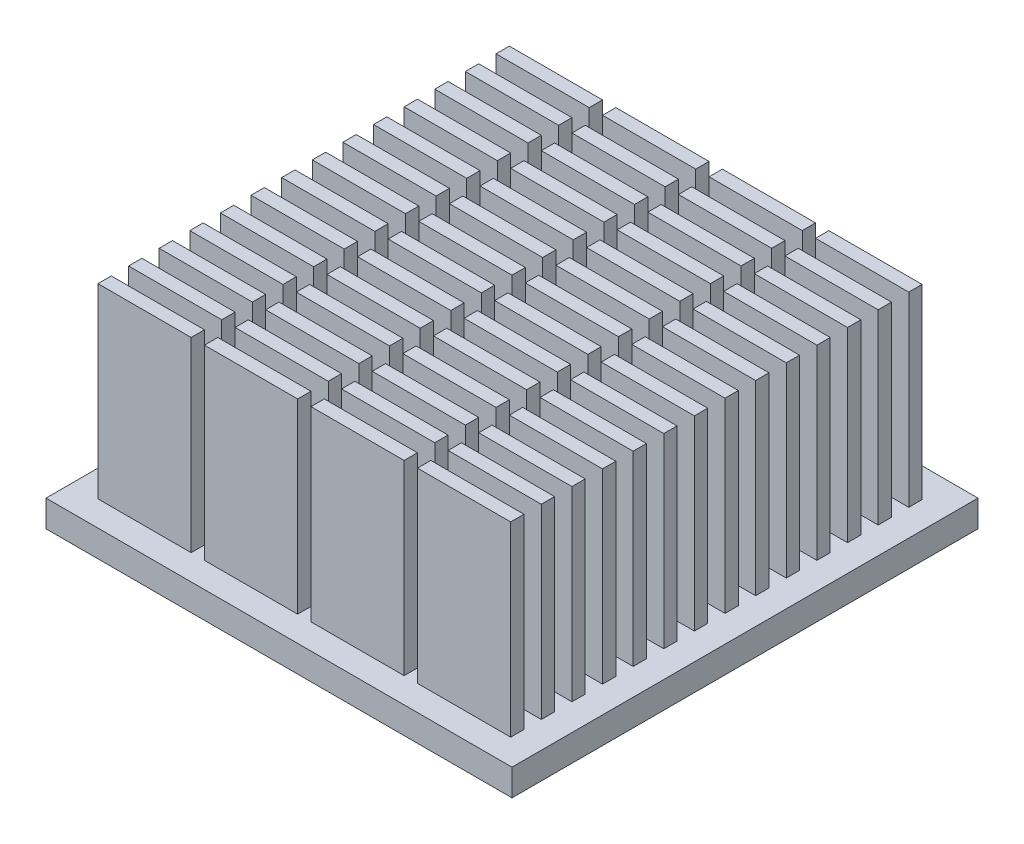
SolidWorks part; units mm, degrees
ref_plane "Front Plane" through (0, 0, 0) normal (0, 0, 1) x (1, 0, 0)
ref_plane "Top Plane" through (0, 0, 0) normal (0, 1, 0) x (1, 0, 0)
ref_plane "Right Plane" through (0, 0, 0) normal (1, 0, 0) x (0, 0, -1)
sketch "Sketch1" plane through (0, 0, 0) normal (0, 1, 0) x (1, 0, 0)
  line L1 (-17.5, -17.5) -> (17.5, -17.5)
  line L2 (-17.5, -17.5) -> (-17.5, 17.5)
  line L3 (-17.5, 17.5) -> (17.5, 17.5)
  line L4 (17.5, -17.5) -> (17.5, 17.5)
  line L5 (-17.5, -17.5) -> (17.5, 17.5) construction
  line L6 (-17.5, 17.5) -> (17.5, -17.5) construction
  point P0 (0, 0)
  dimension "D1" = 35
  dimension "D2" = 35
extrude "Boss-Extrude1" add sketch "Sketch1" along normal blind 2
sketch "Sketch2" plane through (0, 2, 0) normal (0, 1, 0) x (1, 0, 0)
  line L0 (-15.5, -0.8) -> (-8.5, -0.8)
  line L1 (-15.5, 1.5) -> (-8.5, 1.5)
  line L2 (-15.5, 1.5) -> (-15.5, 0.5)
  line L3 (-15.5, 0.5) -> (-8.5, 0.5)
  line L4 (-8.5, 1.5) -> (-8.5, 0.5)
  line L5 (-7.5, 1.5) -> (-0.5, 1.5)
  line L6 (-7.5, 1.5) -> (-7.5, 0.5)
  line L7 (-7.5, 0.5) -> (-0.5, 0.5)
  line L8 (-0.5, 1.5) -> (-0.5, 0.5)
  line L9 (0.5, 1.5) -> (7.5, 1.5)
  line L10 (0.5, 1.5) -> (0.5, 0.5)
  line L11 (0.5, 0.5) -> (7.5, 0.5)
  line L12 (7.5, 1.5) -> (7.5, 0.5)
  line L13 (8.5, 1.5) -> (15.5, 1.5)
  line L14 (8.5, 1.5) -> (8.5, 0.5)
  line L15 (8.5, 0.5) -> (15.5, 0.5)
  line L16 (15.5, 1.5) -> (15.5, 0.5)
  line L17 (-15.5, -0.8) -> (-15.5, -1.8)
  line L18 (-15.5, -1.8) -> (-8.5, -1.8)
  line L19 (-8.5, -0.8) -> (-8.5, -1.8)
  line L20 (-7.5, -0.8) -> (-0.5, -0.8)
  line L21 (-7.5, -0.8) -> (-7.5, -1.8)
  line L22 (-7.5, -1.8) -> (-0.5, -1.8)
  line L23 (-0.5, -0.8) -> (-0.5, -1.8)
  line L24 (0.5, -0.8) -> (7.5, -0.8)
  line L25 (0.5, -0.8) -> (0.5, -1.8)
  line L26 (0.5, -1.8) -> (7.5, -1.8)
  line L27 (7.5, -0.8) -> (7.5, -1.8)
  line L28 (8.5, -0.8) -> (15.5, -0.8)
  line L29 (8.5, -0.8) -> (8.5, -1.8)
  line L30 (8.5, -1.8) -> (15.5, -1.8)
  line L31 (15.5, -0.8) -> (15.5, -1.8)
  line L32 (-15.5, -3.1) -> (-8.5, -3.1)
  line L33 (-15.5, -3.1) -> (-15.5, -4.1)
  line L34 (-15.5, -4.1) -> (-8.5, -4.1)
  line L35 (-8.5, -3.1) -> (-8.5, -4.1)
  line L36 (-7.5, -3.1) -> (-0.5, -3.1)
  line L37 (-7.5, -3.1) -> (-7.5, -4.1)
  line L38 (-7.5, -4.1) -> (-0.5, -4.1)
  line L39 (-0.5, -3.1) -> (-0.5, -4.1)
  line L40 (0.5, -3.1) -> (7.5, -3.1)
  line L41 (0.5, -3.1) -> (0.5, -4.1)
  line L42 (0.5, -4.1) -> (7.5, -4.1)
  line L43 (7.5, -3.1) -> (7.5, -4.1)
  line L44 (8.5, -3.1) -> (15.5, -3.1)
  line L45 (8.5, -3.1) -> (8.5, -4.1)
  line L46 (8.5, -4.1) -> (15.5, -4.1)
  line L47 (15.5, -3.1) -> (15.5, -4.1)
  line L48 (-15.5, -5.4) -> (-8.5, -5.4)
  line L49 (-15.5, -5.4) -> (-15.5, -6.4)
  line L50 (-15.5, -6.4) -> (-8.5, -6.4)
  line L51 (-8.5, -5.4) -> (-8.5, -6.4)
  line L52 (-7.5, -5.4) -> (-0.5, -5.4)
  line L53 (-7.5, -5.4) -> (-7.5, -6.4)
  line L54 (-7.5, -6.4) -> (-0.5, -6.4)
  line L55 (-0.5, -5.4) -> (-0.5, -6.4)
  line L56 (0.5, -5.4) -> (7.5, -5.4)
  line L57 (0.5, -5.4) -> (0.5, -6.4)
  line L58 (0.5, -6.4) -> (7.5, -6.4)
  line L59 (7.5, -5.4) -> (7.5, -6.4)
  line L60 (8.5, -5.4) -> (15.5, -5.4)
  line L61 (8.5, -5.4) -> (8.5, -6.4)
  line L62 (8.5, -6.4) -> (15.5, -6.4)
  line L63 (15.5, -5.4) -> (15.5, -6.4)
  line L64 (-15.5, -7.7) -> (-8.5, -7.7)
  line L65 (-15.5, -7.7) -> (-15.5, -8.7)
  line L66 (-15.5, -8.7) -> (-8.5, -8.7)
  line L67 (-8.5, -7.7) -> (-8.5, -8.7)
  line L68 (-7.5, -7.7) -> (-0.5, -7.7)
  line L69 (-7.5, -7.7) -> (-7.5, -8.7)
  line L70 (-7.5, -8.7) -> (-0.5, -8.7)
  line L71 (-0.5, -7.7) -> (-0.5, -8.7)
  line L72 (0.5, -7.7) -> (7.5, -7.7)
  line L73 (0.5, -7.7) -> (0.5, -8.7)
  line L74 (0.5, -8.7) -> (7.5, -8.7)
  line L75 (7.5, -7.7) -> (7.5, -8.7)
  line L76 (8.5, -7.7) -> (15.5, -7.7)
  line L77 (8.5, -7.7) -> (8.5, -8.7)
  line L78 (8.5, -8.7) -> (15.5, -8.7)
  line L79 (15.5, -7.7) -> (15.5, -8.7)
  line L80 (-15.5, -10) -> (-8.5, -10)
  line L81 (-15.5, -10) -> (-15.5, -11)
  line L82 (-15.5, -11) -> (-8.5, -11)
  line L83 (-8.5, -10) -> (-8.5, -11)
  line L84 (-7.5, -10) -> (-0.5, -10)
  line L85 (-7.5, -10) -> (-7.5, -11)
  line L86 (-7.5, -11) -> (-0.5, -11)
  line L87 (-0.5, -10) -> (-0.5, -11)
  line L88 (0.5, -10) -> (7.5, -10)
  line L89 (0.5, -10) -> (0.5, -11)
  line L90 (0.5, -11) -> (7.5, -11)
  line L91 (7.5, -10) -> (7.5, -11)
  line L92 (8.5, -10) -> (15.5, -10)
  line L93 (8.5, -10) -> (8.5, -11)
  line L94 (8.5, -11) -> (15.5, -11)
  line L95 (15.5, -10) -> (15.5, -11)
  line L96 (-15.5, -12.3) -> (-8.5, -12.3)
  line L97 (-15.5, -12.3) -> (-15.5, -13.3)
  line L98 (-15.5, -13.3) -> (-8.5, -13.3)
  line L99 (-8.5, -12.3) -> (-8.5, -13.3)
  line L100 (-7.5, -12.3) -> (-0.5, -12.3)
  line L101 (-7.5, -12.3) -> (-7.5, -13.3)
  line L102 (-7.5, -13.3) -> (-0.5, -13.3)
  line L103 (-0.5, -12.3) -> (-0.5, -13.3)
  line L104 (0.5, -12.3) -> (7.5, -12.3)
  line L105 (0.5, -12.3) -> (0.5, -13.3)
  line L106 (0.5, -13.3) -> (7.5, -13.3)
  line L107 (7.5, -12.3) -> (7.5, -13.3)
  line L108 (8.5, -12.3) -> (15.5, -12.3)
  line L109 (8.5, -12.3) -> (8.5, -13.3)
  line L110 (8.5, -13.3) -> (15.5, -13.3)
  line L111 (15.5, -12.3) -> (15.5, -13.3)
  line L112 (-15.5, -14.6) -> (-8.5, -14.6)
  line L113 (-15.5, -14.6) -> (-15.5, -15.6)
  line L114 (-15.5, -15.6) -> (-8.5, -15.6)
  line L115 (-8.5, -14.6) -> (-8.5, -15.6)
  line L116 (-7.5, -14.6) -> (-0.5, -14.6)
  line L117 (-7.5, -14.6) -> (-7.5, -15.6)
  line L118 (-7.5, -15.6) -> (-0.5, -15.6)
  line L119 (-0.5, -14.6) -> (-0.5, -15.6)
  line L120 (0.5, -14.6) -> (7.5, -14.6)
  line L121 (0.5, -14.6) -> (0.5, -15.6)
  line L122 (0.5, -15.6) -> (7.5, -15.6)
  line L123 (7.5, -14.6) -> (7.5, -15.6)
  line L124 (8.5, -14.6) -> (15.5, -14.6)
  line L125 (8.5, -14.6) -> (8.5, -15.6)
  line L126 (8.5, -15.6) -> (15.5, -15.6)
  line L127 (15.5, -14.6) -> (15.5, -15.6)
  line L128 (-15.5, 1.5) -> (-8.5, 1.5)
  line L129 (-15.5, 1.5) -> (-15.5, 0.5)
  line L130 (-15.5, 0.5) -> (-8.5, 0.5)
  line L131 (-8.5, 1.5) -> (-8.5, 0.5)
  line L132 (-7.5, 1.5) -> (-0.5, 1.5)
  line L133 (-7.5, 1.5) -> (-7.5, 0.5)
  line L134 (-7.5, 0.5) -> (-0.5, 0.5)
  line L135 (-0.5, 1.5) -> (-0.5, 0.5)
  line L136 (0.5, 1.5) -> (7.5, 1.5)
  line L137 (0.5, 1.5) -> (0.5, 0.5)
  line L138 (0.5, 0.5) -> (7.5, 0.5)
  line L139 (7.5, 1.5) -> (7.5, 0.5)
  line L140 (8.5, 1.5) -> (15.5, 1.5)
  line L141 (8.5, 1.5) -> (8.5, 0.5)
  line L142 (8.5, 0.5) -> (15.5, 0.5)
  line L143 (15.5, 1.5) -> (15.5, 0.5)
  line L144 (-15.5, -0.8) -> (-8.5, -0.8)
  line L145 (-15.5, -0.8) -> (-15.5, -1.8)
  line L146 (-15.5, -1.8) -> (-8.5, -1.8)
  line L147 (-8.5, -0.8) -> (-8.5, -1.8)
  line L148 (-7.5, -0.8) -> (-0.5, -0.8)
  line L149 (-7.5, -0.8) -> (-7.5, -1.8)
  line L150 (-7.5, -1.8) -> (-0.5, -1.8)
  line L151 (-0.5, -0.8) -> (-0.5, -1.8)
  line L152 (0.5, -0.8) -> (7.5, -0.8)
  line L153 (0.5, -0.8) -> (0.5, -1.8)
  line L154 (0.5, -1.8) -> (7.5, -1.8)
  line L155 (7.5, -0.8) -> (7.5, -1.8)
  line L156 (8.5, -0.8) -> (15.5, -0.8)
  line L157 (8.5, -0.8) -> (8.5, -1.8)
  line L158 (8.5, -1.8) -> (15.5, -1.8)
  line L159 (15.5, -0.8) -> (15.5, -1.8)
  line L160 (-15.5, -3.1) -> (-8.5, -3.1)
  line L161 (-15.5, -3.1) -> (-15.5, -4.1)
  line L162 (-15.5, -4.1) -> (-8.5, -4.1)
  line L163 (-8.5, -3.1) -> (-8.5, -4.1)
  line L164 (-7.5, -3.1) -> (-0.5, -3.1)
  line L165 (-7.5, -3.1) -> (-7.5, -4.1)
  line L166 (-7.5, -4.1) -> (-0.5, -4.1)
  line L167 (-0.5, -3.1) -> (-0.5, -4.1)
  line L168 (0.5, -3.1) -> (7.5, -3.1)
  line L169 (0.5, -3.1) -> (0.5, -4.1)
  line L170 (0.5, -4.1) -> (7.5, -4.1)
  line L171 (7.5, -3.1) -> (7.5, -4.1)
  line L172 (8.5, -3.1) -> (15.5, -3.1)
  line L173 (8.5, -3.1) -> (8.5, -4.1)
  line L174 (8.5, -4.1) -> (15.5, -4.1)
  line L175 (15.5, -3.1) -> (15.5, -4.1)
  line L176 (-15.5, -5.4) -> (-8.5, -5.4)
  line L177 (-15.5, -5.4) -> (-15.5, -6.4)
  line L178 (-15.5, -6.4) -> (-8.5, -6.4)
  line L179 (-8.5, -5.4) -> (-8.5, -6.4)
  line L180 (-7.5, -5.4) -> (-0.5, -5.4)
  line L181 (-7.5, -5.4) -> (-7.5, -6.4)
  line L182 (-7.5, -6.4) -> (-0.5, -6.4)
  line L183 (-0.5, -5.4) -> (-0.5, -6.4)
  line L184 (0.5, -5.4) -> (7.5, -5.4)
  line L185 (0.5, -5.4) -> (0.5, -6.4)
  line L186 (0.5, -6.4) -> (7.5, -6.4)
  line L187 (7.5, -5.4) -> (7.5, -6.4)
  line L188 (8.5, -5.4) -> (15.5, -5.4)
  line L189 (8.5, -5.4) -> (8.5, -6.4)
  line L190 (8.5, -6.4) -> (15.5, -6.4)
  line L191 (15.5, -5.4) -> (15.5, -6.4)
  line L192 (-15.5, -7.7) -> (-8.5, -7.7)
  line L193 (-15.5, -7.7) -> (-15.5, -8.7)
  line L194 (-15.5, -8.7) -> (-8.5, -8.7)
  line L195 (-8.5, -7.7) -> (-8.5, -8.7)
  line L196 (-7.5, -7.7) -> (-0.5, -7.7)
  line L197 (-7.5, -7.7) -> (-7.5, -8.7)
  line L198 (-7.5, -8.7) -> (-0.5, -8.7)
  line L199 (-0.5, -7.7) -> (-0.5, -8.7)
  line L200 (0.5, -7.7) -> (7.5, -7.7)
  line L201 (0.5, -7.7) -> (0.5, -8.7)
  line L202 (0.5, -8.7) -> (7.5, -8.7)
  line L203 (7.5, -7.7) -> (7.5, -8.7)
  line L204 (8.5, -7.7) -> (15.5, -7.7)
  line L205 (8.5, -7.7) -> (8.5, -8.7)
  line L206 (8.5, -8.7) -> (15.5, -8.7)
  line L207 (15.5, -7.7) -> (15.5, -8.7)
  line L208 (-15.5, -10) -> (-8.5, -10)
  line L209 (-15.5, -10) -> (-15.5, -11)
  line L210 (-15.5, -11) -> (-8.5, -11)
  line L211 (-8.5, -10) -> (-8.5, -11)
  line L212 (-7.5, -10) -> (-0.5, -10)
  line L213 (-7.5, -10) -> (-7.5, -11)
  line L214 (-7.5, -11) -> (-0.5, -11)
  line L215 (-0.5, -10) -> (-0.5, -11)
  line L216 (0.5, -10) -> (7.5, -10)
  line L217 (0.5, -10) -> (0.5, -11)
  line L218 (0.5, -11) -> (7.5, -11)
  line L219 (7.5, -10) -> (7.5, -11)
  line L220 (8.5, -10) -> (15.5, -10)
  line L221 (8.5, -10) -> (8.5, -11)
  line L222 (8.5, -11) -> (15.5, -11)
  line L223 (15.5, -10) -> (15.5, -11)
  line L224 (-15.5, -12.3) -> (-8.5, -12.3)
  line L225 (-15.5, -12.3) -> (-15.5, -13.3)
  line L226 (-15.5, -13.3) -> (-8.5, -13.3)
  line L227 (-8.5, -12.3) -> (-8.5, -13.3)
  line L228 (-7.5, -12.3) -> (-0.5, -12.3)
  line L229 (-7.5, -12.3) -> (-7.5, -13.3)
  line L230 (-7.5, -13.3) -> (-0.5, -13.3)
  line L231 (-0.5, -12.3) -> (-0.5, -13.3)
  line L232 (0.5, -12.3) -> (7.5, -12.3)
  line L233 (0.5, -12.3) -> (0.5, -13.3)
  line L234 (0.5, -13.3) -> (7.5, -13.3)
  line L235 (7.5, -12.3) -> (7.5, -13.3)
  line L236 (8.5, -12.3) -> (15.5, -12.3)
  line L237 (8.5, -12.3) -> (8.5, -13.3)
  line L238 (8.5, -13.3) -> (15.5, -13.3)
  line L239 (15.5, -12.3) -> (15.5, -13.3)
  line L240 (-15.5, 3.8) -> (-8.5, 3.8)
  line L241 (-15.5, 3.8) -> (-15.5, 2.8)
  line L242 (-15.5, 2.8) -> (-8.5, 2.8)
  line L243 (-8.5, 3.8) -> (-8.5, 2.8)
  line L244 (-7.5, 3.8) -> (-0.5, 3.8)
  line L245 (-7.5, 3.8) -> (-7.5, 2.8)
  line L246 (-7.5, 2.8) -> (-0.5, 2.8)
  line L247 (-0.5, 3.8) -> (-0.5, 2.8)
  line L248 (0.5, 3.8) -> (7.5, 3.8)
  line L249 (0.5, 3.8) -> (0.5, 2.8)
  line L250 (0.5, 2.8) -> (7.5, 2.8)
  line L251 (7.5, 3.8) -> (7.5, 2.8)
  line L252 (8.5, 3.8) -> (15.5, 3.8)
  line L253 (8.5, 3.8) -> (8.5, 2.8)
  line L254 (8.5, 2.8) -> (15.5, 2.8)
  line L255 (15.5, 3.8) -> (15.5, 2.8)
  line L256 (-15.5, 1.5) -> (-8.5, 1.5)
  line L257 (-15.5, 1.5) -> (-15.5, 0.5)
  line L258 (-15.5, 0.5) -> (-8.5, 0.5)
  line L259 (-8.5, 1.5) -> (-8.5, 0.5)
  line L260 (-7.5, 1.5) -> (-0.5, 1.5)
  line L261 (-7.5, 1.5) -> (-7.5, 0.5)
  line L262 (-7.5, 0.5) -> (-0.5, 0.5)
  line L263 (-0.5, 1.5) -> (-0.5, 0.5)
  line L264 (0.5, 1.5) -> (7.5, 1.5)
  line L265 (0.5, 1.5) -> (0.5, 0.5)
  line L266 (0.5, 0.5) -> (7.5, 0.5)
  line L267 (7.5, 1.5) -> (7.5, 0.5)
  line L268 (8.5, 1.5) -> (15.5, 1.5)
  line L269 (8.5, 1.5) -> (8.5, 0.5)
  line L270 (8.5, 0.5) -> (15.5, 0.5)
  line L271 (15.5, 1.5) -> (15.5, 0.5)
  line L272 (-15.5, -0.8) -> (-8.5, -0.8)
  line L273 (-15.5, -0.8) -> (-15.5, -1.8)
  line L274 (-15.5, -1.8) -> (-8.5, -1.8)
  line L275 (-8.5, -0.8) -> (-8.5, -1.8)
  line L276 (-7.5, -0.8) -> (-0.5, -0.8)
  line L277 (-7.5, -0.8) -> (-7.5, -1.8)
  line L278 (-7.5, -1.8) -> (-0.5, -1.8)
  line L279 (-0.5, -0.8) -> (-0.5, -1.8)
  line L280 (0.5, -0.8) -> (7.5, -0.8)
  line L281 (0.5, -0.8) -> (0.5, -1.8)
  line L282 (0.5, -1.8) -> (7.5, -1.8)
  line L283 (7.5, -0.8) -> (7.5, -1.8)
  line L284 (8.5, -0.8) -> (15.5, -0.8)
  line L285 (8.5, -0.8) -> (8.5, -1.8)
  line L286 (8.5, -1.8) -> (15.5, -1.8)
  line L287 (15.5, -0.8) -> (15.5, -1.8)
  line L288 (-15.5, -3.1) -> (-8.5, -3.1)
  line L289 (-15.5, -3.1) -> (-15.5, -4.1)
  line L290 (-15.5, -4.1) -> (-8.5, -4.1)
  line L291 (-8.5, -3.1) -> (-8.5, -4.1)
  line L292 (-7.5, -3.1) -> (-0.5, -3.1)
  line L293 (-7.5, -3.1) -> (-7.5, -4.1)
  line L294 (-7.5, -4.1) -> (-0.5, -4.1)
  line L295 (-0.5, -3.1) -> (-0.5, -4.1)
  line L296 (0.5, -3.1) -> (7.5, -3.1)
  line L297 (0.5, -3.1) -> (0.5, -4.1)
  line L298 (0.5, -4.1) -> (7.5, -4.1)
  line L299 (7.5, -3.1) -> (7.5, -4.1)
  line L300 (8.5, -3.1) -> (15.5, -3.1)
  line L301 (8.5, -3.1) -> (8.5, -4.1)
  line L302 (8.5, -4.1) -> (15.5, -4.1)
  line L303 (15.5, -3.1) -> (15.5, -4.1)
  line L304 (-15.5, -5.4) -> (-8.5, -5.4)
  line L305 (-15.5, -5.4) -> (-15.5, -6.4)
  line L306 (-15.5, -6.4) -> (-8.5, -6.4)
  line L307 (-8.5, -5.4) -> (-8.5, -6.4)
  line L308 (-7.5, -5.4) -> (-0.5, -5.4)
  line L309 (-7.5, -5.4) -> (-7.5, -6.4)
  line L310 (-7.5, -6.4) -> (-0.5, -6.4)
  line L311 (-0.5, -5.4) -> (-0.5, -6.4)
  line L312 (0.5, -5.4) -> (7.5, -5.4)
  line L313 (0.5, -5.4) -> (0.5, -6.4)
  line L314 (0.5, -6.4) -> (7.5, -6.4)
  line L315 (7.5, -5.4) -> (7.5, -6.4)
  line L316 (8.5, -5.4) -> (15.5, -5.4)
  line L317 (8.5, -5.4) -> (8.5, -6.4)
  line L318 (8.5, -6.4) -> (15.5, -6.4)
  line L319 (15.5, -5.4) -> (15.5, -6.4)
  line L320 (-15.5, -7.7) -> (-8.5, -7.7)
  line L321 (-15.5, -7.7) -> (-15.5, -8.7)
  line L322 (-15.5, -8.7) -> (-8.5, -8.7)
  line L323 (-8.5, -7.7) -> (-8.5, -8.7)
  line L324 (-7.5, -7.7) -> (-0.5, -7.7)
  line L325 (-7.5, -7.7) -> (-7.5, -8.7)
  line L326 (-7.5, -8.7) -> (-0.5, -8.7)
  line L327 (-0.5, -7.7) -> (-0.5, -8.7)
  line L328 (0.5, -7.7) -> (7.5, -7.7)
  line L329 (0.5, -7.7) -> (0.5, -8.7)
  line L330 (0.5, -8.7) -> (7.5, -8.7)
  line L331 (7.5, -7.7) -> (7.5, -8.7)
  line L332 (8.5, -7.7) -> (15.5, -7.7)
  line L333 (8.5, -7.7) -> (8.5, -8.7)
  line L334 (8.5, -8.7) -> (15.5, -8.7)
  line L335 (15.5, -7.7) -> (15.5, -8.7)
  line L336 (-15.5, -10) -> (-8.5, -10)
  line L337 (-15.5, -10) -> (-15.5, -11)
  line L338 (-15.5, -11) -> (-8.5, -11)
  line L339 (-8.5, -10) -> (-8.5, -11)
  line L340 (-7.5, -10) -> (-0.5, -10)
  line L341 (-7.5, -10) -> (-7.5, -11)
  line L342 (-7.5, -11) -> (-0.5, -11)
  line L343 (-0.5, -10) -> (-0.5, -11)
  line L344 (0.5, -10) -> (7.5, -10)
  line L345 (0.5, -10) -> (0.5, -11)
  line L346 (0.5, -11) -> (7.5, -11)
  line L347 (7.5, -10) -> (7.5, -11)
  line L348 (8.5, -10) -> (15.5, -10)
  line L349 (8.5, -10) -> (8.5, -11)
  line L350 (8.5, -11) -> (15.5, -11)
  line L351 (15.5, -10) -> (15.5, -11)
  line L352 (-15.5, 6.1) -> (-8.5, 6.1)
  line L353 (-15.5, 6.1) -> (-15.5, 5.1)
  line L354 (-15.5, 5.1) -> (-8.5, 5.1)
  line L355 (-8.5, 6.1) -> (-8.5, 5.1)
  line L356 (-7.5, 6.1) -> (-0.5, 6.1)
  line L357 (-7.5, 6.1) -> (-7.5, 5.1)
  line L358 (-7.5, 5.1) -> (-0.5, 5.1)
  line L359 (-0.5, 6.1) -> (-0.5, 5.1)
  line L360 (0.5, 6.1) -> (7.5, 6.1)
  line L361 (0.5, 6.1) -> (0.5, 5.1)
  line L362 (0.5, 5.1) -> (7.5, 5.1)
  line L363 (7.5, 6.1) -> (7.5, 5.1)
  line L364 (8.5, 6.1) -> (15.5, 6.1)
  line L365 (8.5, 6.1) -> (8.5, 5.1)
  line L366 (8.5, 5.1) -> (15.5, 5.1)
  line L367 (15.5, 6.1) -> (15.5, 5.1)
  line L368 (-15.5, 3.8) -> (-8.5, 3.8)
  line L369 (-15.5, 3.8) -> (-15.5, 2.8)
  line L370 (-15.5, 2.8) -> (-8.5, 2.8)
  line L371 (-8.5, 3.8) -> (-8.5, 2.8)
  line L372 (-7.5, 3.8) -> (-0.5, 3.8)
  line L373 (-7.5, 3.8) -> (-7.5, 2.8)
  line L374 (-7.5, 2.8) -> (-0.5, 2.8)
  line L375 (-0.5, 3.8) -> (-0.5, 2.8)
  line L376 (0.5, 3.8) -> (7.5, 3.8)
  line L377 (0.5, 3.8) -> (0.5, 2.8)
  line L378 (0.5, 2.8) -> (7.5, 2.8)
  line L379 (7.5, 3.8) -> (7.5, 2.8)
  line L380 (8.5, 3.8) -> (15.5, 3.8)
  line L381 (8.5, 3.8) -> (8.5, 2.8)
  line L382 (8.5, 2.8) -> (15.5, 2.8)
  line L383 (15.5, 3.8) -> (15.5, 2.8)
  line L384 (-15.5, 1.5) -> (-8.5, 1.5)
  line L385 (-15.5, 1.5) -> (-15.5, 0.5)
  line L386 (-15.5, 0.5) -> (-8.5, 0.5)
  line L387 (-8.5, 1.5) -> (-8.5, 0.5)
  line L388 (-7.5, 1.5) -> (-0.5, 1.5)
  line L389 (-7.5, 1.5) -> (-7.5, 0.5)
  line L390 (-7.5, 0.5) -> (-0.5, 0.5)
  line L391 (-0.5, 1.5) -> (-0.5, 0.5)
  line L392 (0.5, 1.5) -> (7.5, 1.5)
  line L393 (0.5, 1.5) -> (0.5, 0.5)
  line L394 (0.5, 0.5) -> (7.5, 0.5)
  line L395 (7.5, 1.5) -> (7.5, 0.5)
  line L396 (8.5, 1.5) -> (15.5, 1.5)
  line L397 (8.5, 1.5) -> (8.5, 0.5)
  line L398 (8.5, 0.5) -> (15.5, 0.5)
  line L399 (15.5, 1.5) -> (15.5, 0.5)
  line L400 (-15.5, -0.8) -> (-8.5, -0.8)
  line L401 (-15.5, -0.8) -> (-15.5, -1.8)
  line L402 (-15.5, -1.8) -> (-8.5, -1.8)
  line L403 (-8.5, -0.8) -> (-8.5, -1.8)
  line L404 (-7.5, -0.8) -> (-0.5, -0.8)
  line L405 (-7.5, -0.8) -> (-7.5, -1.8)
  line L406 (-7.5, -1.8) -> (-0.5, -1.8)
  line L407 (-0.5, -0.8) -> (-0.5, -1.8)
  line L408 (0.5, -0.8) -> (7.5, -0.8)
  line L409 (0.5, -0.8) -> (0.5, -1.8)
  line L410 (0.5, -1.8) -> (7.5, -1.8)
  line L411 (7.5, -0.8) -> (7.5, -1.8)
  line L412 (8.5, -0.8) -> (15.5, -0.8)
  line L413 (8.5, -0.8) -> (8.5, -1.8)
  line L414 (8.5, -1.8) -> (15.5, -1.8)
  line L415 (15.5, -0.8) -> (15.5, -1.8)
  line L416 (-15.5, -3.1) -> (-8.5, -3.1)
  line L417 (-15.5, -3.1) -> (-15.5, -4.1)
  line L418 (-15.5, -4.1) -> (-8.5, -4.1)
  line L419 (-8.5, -3.1) -> (-8.5, -4.1)
  line L420 (-7.5, -3.1) -> (-0.5, -3.1)
  line L421 (-7.5, -3.1) -> (-7.5, -4.1)
  line L422 (-7.5, -4.1) -> (-0.5, -4.1)
  line L423 (-0.5, -3.1) -> (-0.5, -4.1)
  line L424 (0.5, -3.1) -> (7.5, -3.1)
  line L425 (0.5, -3.1) -> (0.5, -4.1)
  line L426 (0.5, -4.1) -> (7.5, -4.1)
  line L427 (7.5, -3.1) -> (7.5, -4.1)
  line L428 (8.5, -3.1) -> (15.5, -3.1)
  line L429 (8.5, -3.1) -> (8.5, -4.1)
  line L430 (8.5, -4.1) -> (15.5, -4.1)
  line L431 (15.5, -3.1) -> (15.5, -4.1)
  line L432 (-15.5, -5.4) -> (-8.5, -5.4)
  line L433 (-15.5, -5.4) -> (-15.5, -6.4)
  line L434 (-15.5, -6.4) -> (-8.5, -6.4)
  line L435 (-8.5, -5.4) -> (-8.5, -6.4)
  line L436 (-7.5, -5.4) -> (-0.5, -5.4)
  line L437 (-7.5, -5.4) -> (-7.5, -6.4)
  line L438 (-7.5, -6.4) -> (-0.5, -6.4)
  line L439 (-0.5, -5.4) -> (-0.5, -6.4)
  line L440 (0.5, -5.4) -> (7.5, -5.4)
  line L441 (0.5, -5.4) -> (0.5, -6.4)
  line L442 (0.5, -6.4) -> (7.5, -6.4)
  line L443 (7.5, -5.4) -> (7.5, -6.4)
  line L444 (8.5, -5.4) -> (15.5, -5.4)
  line L445 (8.5, -5.4) -> (8.5, -6.4)
  line L446 (8.5, -6.4) -> (15.5, -6.4)
  line L447 (15.5, -5.4) -> (15.5, -6.4)
  line L448 (-15.5, -7.7) -> (-8.5, -7.7)
  line L449 (-15.5, -7.7) -> (-15.5, -8.7)
  line L450 (-15.5, -8.7) -> (-8.5, -8.7)
  line L451 (-8.5, -7.7) -> (-8.5, -8.7)
  line L452 (-7.5, -7.7) -> (-0.5, -7.7)
  line L453 (-7.5, -7.7) -> (-7.5, -8.7)
  line L454 (-7.5, -8.7) -> (-0.5, -8.7)
  line L455 (-0.5, -7.7) -> (-0.5, -8.7)
  line L456 (0.5, -7.7) -> (7.5, -7.7)
  line L457 (0.5, -7.7) -> (0.5, -8.7)
  line L458 (0.5, -8.7) -> (7.5, -8.7)
  line L459 (7.5, -7.7) -> (7.5, -8.7)
  line L460 (8.5, -7.7) -> (15.5, -7.7)
  line L461 (8.5, -7.7) -> (8.5, -8.7)
  line L462 (8.5, -8.7) -> (15.5, -8.7)
  line L463 (15.5, -7.7) -> (15.5, -8.7)
  line L464 (-15.5, 8.4) -> (-8.5, 8.4)
  line L465 (-15.5, 8.4) -> (-15.5, 7.4)
  line L466 (-15.5, 7.4) -> (-8.5, 7.4)
  line L467 (-8.5, 8.4) -> (-8.5, 7.4)
  line L468 (-7.5, 8.4) -> (-0.5, 8.4)
  line L469 (-7.5, 8.4) -> (-7.5, 7.4)
  line L470 (-7.5, 7.4) -> (-0.5, 7.4)
  line L471 (-0.5, 8.4) -> (-0.5, 7.4)
  line L472 (0.5, 8.4) -> (7.5, 8.4)
  line L473 (0.5, 8.4) -> (0.5, 7.4)
  line L474 (0.5, 7.4) -> (7.5, 7.4)
  line L475 (7.5, 8.4) -> (7.5, 7.4)
  line L476 (8.5, 8.4) -> (15.5, 8.4)
  line L477 (8.5, 8.4) -> (8.5, 7.4)
  line L478 (8.5, 7.4) -> (15.5, 7.4)
  line L479 (15.5, 8.4) -> (15.5, 7.4)
  line L480 (-15.5, 6.1) -> (-8.5, 6.1)
  line L481 (-15.5, 6.1) -> (-15.5, 5.1)
  line L482 (-15.5, 5.1) -> (-8.5, 5.1)
  line L483 (-8.5, 6.1) -> (-8.5, 5.1)
  line L484 (-7.5, 6.1) -> (-0.5, 6.1)
  line L485 (-7.5, 6.1) -> (-7.5, 5.1)
  line L486 (-7.5, 5.1) -> (-0.5, 5.1)
  line L487 (-0.5, 6.1) -> (-0.5, 5.1)
  line L488 (0.5, 6.1) -> (7.5, 6.1)
  line L489 (0.5, 6.1) -> (0.5, 5.1)
  line L490 (0.5, 5.1) -> (7.5, 5.1)
  line L491 (7.5, 6.1) -> (7.5, 5.1)
  line L492 (8.5, 6.1) -> (15.5, 6.1)
  line L493 (8.5, 6.1) -> (8.5, 5.1)
  line L494 (8.5, 5.1) -> (15.5, 5.1)
  line L495 (15.5, 6.1) -> (15.5, 5.1)
  line L496 (-15.5, 3.8) -> (-8.5, 3.8)
  line L497 (-15.5, 3.8) -> (-15.5, 2.8)
  line L498 (-15.5, 2.8) -> (-8.5, 2.8)
  line L499 (-8.5, 3.8) -> (-8.5, 2.8)
  line L500 (-7.5, 3.8) -> (-0.5, 3.8)
  line L501 (-7.5, 3.8) -> (-7.5, 2.8)
  line L502 (-7.5, 2.8) -> (-0.5, 2.8)
  line L503 (-0.5, 3.8) -> (-0.5, 2.8)
  line L504 (0.5, 3.8) -> (7.5, 3.8)
  line L505 (0.5, 3.8) -> (0.5, 2.8)
  line L506 (0.5, 2.8) -> (7.5, 2.8)
  line L507 (7.5, 3.8) -> (7.5, 2.8)
  line L508 (8.5, 3.8) -> (15.5, 3.8)
  line L509 (8.5, 3.8) -> (8.5, 2.8)
  line L510 (8.5, 2.8) -> (15.5, 2.8)
  line L511 (15.5, 3.8) -> (15.5, 2.8)
  line L512 (-15.5, 1.5) -> (-8.5, 1.5)
  line L513 (-15.5, 1.5) -> (-15.5, 0.5)
  line L514 (-15.5, 0.5) -> (-8.5, 0.5)
  line L515 (-8.5, 1.5) -> (-8.5, 0.5)
  line L516 (-7.5, 1.5) -> (-0.5, 1.5)
  line L517 (-7.5, 1.5) -> (-7.5, 0.5)
  line L518 (-7.5, 0.5) -> (-0.5, 0.5)
  line L519 (-0.5, 1.5) -> (-0.5, 0.5)
  line L520 (0.5, 1.5) -> (7.5, 1.5)
  line L521 (0.5, 1.5) -> (0.5, 0.5)
  line L522 (0.5, 0.5) -> (7.5, 0.5)
  line L523 (7.5, 1.5) -> (7.5, 0.5)
  line L524 (8.5, 1.5) -> (15.5, 1.5)
  line L525 (8.5, 1.5) -> (8.5, 0.5)
  line L526 (8.5, 0.5) -> (15.5, 0.5)
  line L527 (15.5, 1.5) -> (15.5, 0.5)
  line L528 (-15.5, -0.8) -> (-8.5, -0.8)
  line L529 (-15.5, -0.8) -> (-15.5, -1.8)
  line L530 (-15.5, -1.8) -> (-8.5, -1.8)
  line L531 (-8.5, -0.8) -> (-8.5, -1.8)
  line L532 (-7.5, -0.8) -> (-0.5, -0.8)
  line L533 (-7.5, -0.8) -> (-7.5, -1.8)
  line L534 (-7.5, -1.8) -> (-0.5, -1.8)
  line L535 (-0.5, -0.8) -> (-0.5, -1.8)
  line L536 (0.5, -0.8) -> (7.5, -0.8)
  line L537 (0.5, -0.8) -> (0.5, -1.8)
  line L538 (0.5, -1.8) -> (7.5, -1.8)
  line L539 (7.5, -0.8) -> (7.5, -1.8)
  line L540 (8.5, -0.8) -> (15.5, -0.8)
  line L541 (8.5, -0.8) -> (8.5, -1.8)
  line L542 (8.5, -1.8) -> (15.5, -1.8)
  line L543 (15.5, -0.8) -> (15.5, -1.8)
  line L544 (-15.5, -3.1) -> (-8.5, -3.1)
  line L545 (-15.5, -3.1) -> (-15.5, -4.1)
  line L546 (-15.5, -4.1) -> (-8.5, -4.1)
  line L547 (-8.5, -3.1) -> (-8.5, -4.1)
  line L548 (-7.5, -3.1) -> (-0.5, -3.1)
  line L549 (-7.5, -3.1) -> (-7.5, -4.1)
  line L550 (-7.5, -4.1) -> (-0.5, -4.1)
  line L551 (-0.5, -3.1) -> (-0.5, -4.1)
  line L552 (0.5, -3.1) -> (7.5, -3.1)
  line L553 (0.5, -3.1) -> (0.5, -4.1)
  line L554 (0.5, -4.1) -> (7.5, -4.1)
  line L555 (7.5, -3.1) -> (7.5, -4.1)
  line L556 (8.5, -3.1) -> (15.5, -3.1)
  line L557 (8.5, -3.1) -> (8.5, -4.1)
  line L558 (8.5, -4.1) -> (15.5, -4.1)
  line L559 (15.5, -3.1) -> (15.5, -4.1)
  line L560 (-15.5, -5.4) -> (-8.5, -5.4)
  line L561 (-15.5, -5.4) -> (-15.5, -6.4)
  line L562 (-15.5, -6.4) -> (-8.5, -6.4)
  line L563 (-8.5, -5.4) -> (-8.5, -6.4)
  line L564 (-7.5, -5.4) -> (-0.5, -5.4)
  line L565 (-7.5, -5.4) -> (-7.5, -6.4)
  line L566 (-7.5, -6.4) -> (-0.5, -6.4)
  line L567 (-0.5, -5.4) -> (-0.5, -6.4)
  line L568 (0.5, -5.4) -> (7.5, -5.4)
  line L569 (0.5, -5.4) -> (0.5, -6.4)
  line L570 (0.5, -6.4) -> (7.5, -6.4)
  line L571 (7.5, -5.4) -> (7.5, -6.4)
  line L572 (8.5, -5.4) -> (15.5, -5.4)
  line L573 (8.5, -5.4) -> (8.5, -6.4)
  line L574 (8.5, -6.4) -> (15.5, -6.4)
  line L575 (15.5, -5.4) -> (15.5, -6.4)
  line L576 (-15.5, 10.7) -> (-8.5, 10.7)
  line L577 (-15.5, 10.7) -> (-15.5, 9.7)
  line L578 (-15.5, 9.7) -> (-8.5, 9.7)
  line L579 (-8.5, 10.7) -> (-8.5, 9.7)
  line L580 (-7.5, 10.7) -> (-0.5, 10.7)
  line L581 (-7.5, 10.7) -> (-7.5, 9.7)
  line L582 (-7.5, 9.7) -> (-0.5, 9.7)
  line L583 (-0.5, 10.7) -> (-0.5, 9.7)
  line L584 (0.5, 10.7) -> (7.5, 10.7)
  line L585 (0.5, 10.7) -> (0.5, 9.7)
  line L586 (0.5, 9.7) -> (7.5, 9.7)
  line L587 (7.5, 10.7) -> (7.5, 9.7)
  line L588 (8.5, 10.7) -> (15.5, 10.7)
  line L589 (8.5, 10.7) -> (8.5, 9.7)
  line L590 (8.5, 9.7) -> (15.5, 9.7)
  line L591 (15.5, 10.7) -> (15.5, 9.7)
  line L592 (-15.5, 8.4) -> (-8.5, 8.4)
  line L593 (-15.5, 8.4) -> (-15.5, 7.4)
  line L594 (-15.5, 7.4) -> (-8.5, 7.4)
  line L595 (-8.5, 8.4) -> (-8.5, 7.4)
  line L596 (-7.5, 8.4) -> (-0.5, 8.4)
  line L597 (-7.5, 8.4) -> (-7.5, 7.4)
  line L598 (-7.5, 7.4) -> (-0.5, 7.4)
  line L599 (-0.5, 8.4) -> (-0.5, 7.4)
  line L600 (0.5, 8.4) -> (7.5, 8.4)
  line L601 (0.5, 8.4) -> (0.5, 7.4)
  line L602 (0.5, 7.4) -> (7.5, 7.4)
  line L603 (7.5, 8.4) -> (7.5, 7.4)
  line L604 (8.5, 8.4) -> (15.5, 8.4)
  line L605 (8.5, 8.4) -> (8.5, 7.4)
  line L606 (8.5, 7.4) -> (15.5, 7.4)
  line L607 (15.5, 8.4) -> (15.5, 7.4)
  line L608 (-15.5, 6.1) -> (-8.5, 6.1)
  line L609 (-15.5, 6.1) -> (-15.5, 5.1)
  line L610 (-15.5, 5.1) -> (-8.5, 5.1)
  line L611 (-8.5, 6.1) -> (-8.5, 5.1)
  line L612 (-7.5, 6.1) -> (-0.5, 6.1)
  line L613 (-7.5, 6.1) -> (-7.5, 5.1)
  line L614 (-7.5, 5.1) -> (-0.5, 5.1)
  line L615 (-0.5, 6.1) -> (-0.5, 5.1)
  line L616 (0.5, 6.1) -> (7.5, 6.1)
  line L617 (0.5, 6.1) -> (0.5, 5.1)
  line L618 (0.5, 5.1) -> (7.5, 5.1)
  line L619 (7.5, 6.1) -> (7.5, 5.1)
  line L620 (8.5, 6.1) -> (15.5, 6.1)
  line L621 (8.5, 6.1) -> (8.5, 5.1)
  line L622 (8.5, 5.1) -> (15.5, 5.1)
  line L623 (15.5, 6.1) -> (15.5, 5.1)
  line L624 (-15.5, 3.8) -> (-8.5, 3.8)
  line L625 (-15.5, 3.8) -> (-15.5, 2.8)
  line L626 (-15.5, 2.8) -> (-8.5, 2.8)
  line L627 (-8.5, 3.8) -> (-8.5, 2.8)
  line L628 (-7.5, 3.8) -> (-0.5, 3.8)
  line L629 (-7.5, 3.8) -> (-7.5, 2.8)
  line L630 (-7.5, 2.8) -> (-0.5, 2.8)
  line L631 (-0.5, 3.8) -> (-0.5, 2.8)
  line L632 (0.5, 3.8) -> (7.5, 3.8)
  line L633 (0.5, 3.8) -> (0.5, 2.8)
  line L634 (0.5, 2.8) -> (7.5, 2.8)
  line L635 (7.5, 3.8) -> (7.5, 2.8)
  line L636 (8.5, 3.8) -> (15.5, 3.8)
  line L637 (8.5, 3.8) -> (8.5, 2.8)
  line L638 (8.5, 2.8) -> (15.5, 2.8)
  line L639 (15.5, 3.8) -> (15.5, 2.8)
  line L640 (-15.5, 1.5) -> (-8.5, 1.5)
  line L641 (-15.5, 1.5) -> (-15.5, 0.5)
  line L642 (-15.5, 0.5) -> (-8.5, 0.5)
  line L643 (-8.5, 1.5) -> (-8.5, 0.5)
  line L644 (-7.5, 1.5) -> (-0.5, 1.5)
  line L645 (-7.5, 1.5) -> (-7.5, 0.5)
  line L646 (-7.5, 0.5) -> (-0.5, 0.5)
  line L647 (-0.5, 1.5) -> (-0.5, 0.5)
  line L648 (0.5, 1.5) -> (7.5, 1.5)
  line L649 (0.5, 1.5) -> (0.5, 0.5)
  line L650 (0.5, 0.5) -> (7.5, 0.5)
  line L651 (7.5, 1.5) -> (7.5, 0.5)
  line L652 (8.5, 1.5) -> (15.5, 1.5)
  line L653 (8.5, 1.5) -> (8.5, 0.5)
  line L654 (8.5, 0.5) -> (15.5, 0.5)
  line L655 (15.5, 1.5) -> (15.5, 0.5)
  line L656 (-15.5, -0.8) -> (-8.5, -0.8)
  line L657 (-15.5, -0.8) -> (-15.5, -1.8)
  line L658 (-15.5, -1.8) -> (-8.5, -1.8)
  line L659 (-8.5, -0.8) -> (-8.5, -1.8)
  line L660 (-7.5, -0.8) -> (-0.5, -0.8)
  line L661 (-7.5, -0.8) -> (-7.5, -1.8)
  line L662 (-7.5, -1.8) -> (-0.5, -1.8)
  line L663 (-0.5, -0.8) -> (-0.5, -1.8)
  line L664 (0.5, -0.8) -> (7.5, -0.8)
  line L665 (0.5, -0.8) -> (0.5, -1.8)
  line L666 (0.5, -1.8) -> (7.5, -1.8)
  line L667 (7.5, -0.8) -> (7.5, -1.8)
  line L668 (8.5, -0.8) -> (15.5, -0.8)
  line L669 (8.5, -0.8) -> (8.5, -1.8)
  line L670 (8.5, -1.8) -> (15.5, -1.8)
  line L671 (15.5, -0.8) -> (15.5, -1.8)
  line L672 (-15.5, -3.1) -> (-8.5, -3.1)
  line L673 (-15.5, -3.1) -> (-15.5, -4.1)
  line L674 (-15.5, -4.1) -> (-8.5, -4.1)
  line L675 (-8.5, -3.1) -> (-8.5, -4.1)
  line L676 (-7.5, -3.1) -> (-0.5, -3.1)
  line L677 (-7.5, -3.1) -> (-7.5, -4.1)
  line L678 (-7.5, -4.1) -> (-0.5, -4.1)
  line L679 (-0.5, -3.1) -> (-0.5, -4.1)
  line L680 (0.5, -3.1) -> (7.5, -3.1)
  line L681 (0.5, -3.1) -> (0.5, -4.1)
  line L682 (0.5, -4.1) -> (7.5, -4.1)
  line L683 (7.5, -3.1) -> (7.5, -4.1)
  line L684 (8.5, -3.1) -> (15.5, -3.1)
  line L685 (8.5, -3.1) -> (8.5, -4.1)
  line L686 (8.5, -4.1) -> (15.5, -4.1)
  line L687 (15.5, -3.1) -> (15.5, -4.1)
  line L688 (-15.5, 13) -> (-8.5, 13)
  line L689 (-15.5, 13) -> (-15.5, 12)
  line L690 (-15.5, 12) -> (-8.5, 12)
  line L691 (-8.5, 13) -> (-8.5, 12)
  line L692 (-7.5, 13) -> (-0.5, 13)
  line L693 (-7.5, 13) -> (-7.5, 12)
  line L694 (-7.5, 12) -> (-0.5, 12)
  line L695 (-0.5, 13) -> (-0.5, 12)
  line L696 (0.5, 13) -> (7.5, 13)
  line L697 (0.5, 13) -> (0.5, 12)
  line L698 (0.5, 12) -> (7.5, 12)
  line L699 (7.5, 13) -> (7.5, 12)
  line L700 (8.5, 13) -> (15.5, 13)
  line L701 (8.5, 13) -> (8.5, 12)
  line L702 (8.5, 12) -> (15.5, 12)
  line L703 (15.5, 13) -> (15.5, 12)
  line L704 (-15.5, 10.7) -> (-8.5, 10.7)
  line L705 (-15.5, 10.7) -> (-15.5, 9.7)
  line L706 (-15.5, 9.7) -> (-8.5, 9.7)
  line L707 (-8.5, 10.7) -> (-8.5, 9.7)
  line L708 (-7.5, 10.7) -> (-0.5, 10.7)
  line L709 (-7.5, 10.7) -> (-7.5, 9.7)
  line L710 (-7.5, 9.7) -> (-0.5, 9.7)
  line L711 (-0.5, 10.7) -> (-0.5, 9.7)
  line L712 (0.5, 10.7) -> (7.5, 10.7)
  line L713 (0.5, 10.7) -> (0.5, 9.7)
  line L714 (0.5, 9.7) -> (7.5, 9.7)
  line L715 (7.5, 10.7) -> (7.5, 9.7)
  line L716 (8.5, 10.7) -> (15.5, 10.7)
  line L717 (8.5, 10.7) -> (8.5, 9.7)
  line L718 (8.5, 9.7) -> (15.5, 9.7)
  line L719 (15.5, 10.7) -> (15.5, 9.7)
  line L720 (-15.5, 8.4) -> (-8.5, 8.4)
  line L721 (-15.5, 8.4) -> (-15.5, 7.4)
  line L722 (-15.5, 7.4) -> (-8.5, 7.4)
  line L723 (-8.5, 8.4) -> (-8.5, 7.4)
  line L724 (-7.5, 8.4) -> (-0.5, 8.4)
  line L725 (-7.5, 8.4) -> (-7.5, 7.4)
  line L726 (-7.5, 7.4) -> (-0.5, 7.4)
  line L727 (-0.5, 8.4) -> (-0.5, 7.4)
  line L728 (0.5, 8.4) -> (7.5, 8.4)
  line L729 (0.5, 8.4) -> (0.5, 7.4)
  line L730 (0.5, 7.4) -> (7.5, 7.4)
  line L731 (7.5, 8.4) -> (7.5, 7.4)
  line L732 (8.5, 8.4) -> (15.5, 8.4)
  line L733 (8.5, 8.4) -> (8.5, 7.4)
  line L734 (8.5, 7.4) -> (15.5, 7.4)
  line L735 (15.5, 8.4) -> (15.5, 7.4)
  line L736 (-15.5, 6.1) -> (-8.5, 6.1)
  line L737 (-15.5, 6.1) -> (-15.5, 5.1)
  line L738 (-15.5, 5.1) -> (-8.5, 5.1)
  line L739 (-8.5, 6.1) -> (-8.5, 5.1)
  line L740 (-7.5, 6.1) -> (-0.5, 6.1)
  line L741 (-7.5, 6.1) -> (-7.5, 5.1)
  line L742 (-7.5, 5.1) -> (-0.5, 5.1)
  line L743 (-0.5, 6.1) -> (-0.5, 5.1)
  line L744 (0.5, 6.1) -> (7.5, 6.1)
  line L745 (0.5, 6.1) -> (0.5, 5.1)
  line L746 (0.5, 5.1) -> (7.5, 5.1)
  line L747 (7.5, 6.1) -> (7.5, 5.1)
  line L748 (8.5, 6.1) -> (15.5, 6.1)
  line L749 (8.5, 6.1) -> (8.5, 5.1)
  line L750 (8.5, 5.1) -> (15.5, 5.1)
  line L751 (15.5, 6.1) -> (15.5, 5.1)
  line L752 (-15.5, 3.8) -> (-8.5, 3.8)
  line L753 (-15.5, 3.8) -> (-15.5, 2.8)
  line L754 (-15.5, 2.8) -> (-8.5, 2.8)
  line L755 (-8.5, 3.8) -> (-8.5, 2.8)
  line L756 (-7.5, 3.8) -> (-0.5, 3.8)
  line L757 (-7.5, 3.8) -> (-7.5, 2.8)
  line L758 (-7.5, 2.8) -> (-0.5, 2.8)
  line L759 (-0.5, 3.8) -> (-0.5, 2.8)
  line L760 (0.5, 3.8) -> (7.5, 3.8)
  line L761 (0.5, 3.8) -> (0.5, 2.8)
  line L762 (0.5, 2.8) -> (7.5, 2.8)
  line L763 (7.5, 3.8) -> (7.5, 2.8)
  line L764 (8.5, 3.8) -> (15.5, 3.8)
  line L765 (8.5, 3.8) -> (8.5, 2.8)
  line L766 (8.5, 2.8) -> (15.5, 2.8)
  line L767 (15.5, 3.8) -> (15.5, 2.8)
  line L768 (-15.5, 1.5) -> (-8.5, 1.5)
  line L769 (-15.5, 1.5) -> (-15.5, 0.5)
  line L770 (-15.5, 0.5) -> (-8.5, 0.5)
  line L771 (-8.5, 1.5) -> (-8.5, 0.5)
  line L772 (-7.5, 1.5) -> (-0.5, 1.5)
  line L773 (-7.5, 1.5) -> (-7.5, 0.5)
  line L774 (-7.5, 0.5) -> (-0.5, 0.5)
  line L775 (-0.5, 1.5) -> (-0.5, 0.5)
  line L776 (0.5, 1.5) -> (7.5, 1.5)
  line L777 (0.5, 1.5) -> (0.5, 0.5)
  line L778 (0.5, 0.5) -> (7.5, 0.5)
  line L779 (7.5, 1.5) -> (7.5, 0.5)
  line L780 (8.5, 1.5) -> (15.5, 1.5)
  line L781 (8.5, 1.5) -> (8.5, 0.5)
  line L782 (8.5, 0.5) -> (15.5, 0.5)
  line L783 (15.5, 1.5) -> (15.5, 0.5)
  line L784 (-15.5, -0.8) -> (-8.5, -0.8)
  line L785 (-15.5, -0.8) -> (-15.5, -1.8)
  line L786 (-15.5, -1.8) -> (-8.5, -1.8)
  line L787 (-8.5, -0.8) -> (-8.5, -1.8)
  line L788 (-7.5, -0.8) -> (-0.5, -0.8)
  line L789 (-7.5, -0.8) -> (-7.5, -1.8)
  line L790 (-7.5, -1.8) -> (-0.5, -1.8)
  line L791 (-0.5, -0.8) -> (-0.5, -1.8)
  line L792 (0.5, -0.8) -> (7.5, -0.8)
  line L793 (0.5, -0.8) -> (0.5, -1.8)
  line L794 (0.5, -1.8) -> (7.5, -1.8)
  line L795 (7.5, -0.8) -> (7.5, -1.8)
  line L796 (8.5, -0.8) -> (15.5, -0.8)
  line L797 (8.5, -0.8) -> (8.5, -1.8)
  line L798 (8.5, -1.8) -> (15.5, -1.8)
  line L799 (15.5, -0.8) -> (15.5, -1.8)
  line L800 (-15.5, 3.8) -> (-8.5, 3.8)
  line L801 (-15.5, 3.8) -> (-15.5, 2.8)
  line L802 (-15.5, 2.8) -> (-8.5, 2.8)
  line L803 (-8.5, 3.8) -> (-8.5, 2.8)
  line L804 (-7.5, 3.8) -> (-0.5, 3.8)
  line L805 (-7.5, 3.8) -> (-7.5, 2.8)
  line L806 (-7.5, 2.8) -> (-0.5, 2.8)
  line L807 (-0.5, 3.8) -> (-0.5, 2.8)
  line L808 (0.5, 3.8) -> (7.5, 3.8)
  line L809 (0.5, 3.8) -> (0.5, 2.8)
  line L810 (0.5, 2.8) -> (7.5, 2.8)
  line L811 (7.5, 3.8) -> (7.5, 2.8)
  line L812 (8.5, 3.8) -> (15.5, 3.8)
  line L813 (8.5, 3.8) -> (8.5, 2.8)
  line L814 (8.5, 2.8) -> (15.5, 2.8)
  line L815 (15.5, 3.8) -> (15.5, 2.8)
  line L816 (-15.5, 6.1) -> (-8.5, 6.1)
  line L817 (-15.5, 6.1) -> (-15.5, 5.1)
  line L818 (-15.5, 5.1) -> (-8.5, 5.1)
  line L819 (-8.5, 6.1) -> (-8.5, 5.1)
  line L820 (-7.5, 6.1) -> (-0.5, 6.1)
  line L821 (-7.5, 6.1) -> (-7.5, 5.1)
  line L822 (-7.5, 5.1) -> (-0.5, 5.1)
  line L823 (-0.5, 6.1) -> (-0.5, 5.1)
  line L824 (0.5, 6.1) -> (7.5, 6.1)
  line L825 (0.5, 6.1) -> (0.5, 5.1)
  line L826 (0.5, 5.1) -> (7.5, 5.1)
  line L827 (7.5, 6.1) -> (7.5, 5.1)
  line L828 (8.5, 6.1) -> (15.5, 6.1)
  line L829 (8.5, 6.1) -> (8.5, 5.1)
  line L830 (8.5, 5.1) -> (15.5, 5.1)
  line L831 (15.5, 6.1) -> (15.5, 5.1)
  line L832 (-15.5, 8.4) -> (-8.5, 8.4)
  line L833 (-15.5, 8.4) -> (-15.5, 7.4)
  line L834 (-15.5, 7.4) -> (-8.5, 7.4)
  line L835 (-8.5, 8.4) -> (-8.5, 7.4)
  line L836 (-7.5, 8.4) -> (-0.5, 8.4)
  line L837 (-7.5, 8.4) -> (-7.5, 7.4)
  line L838 (-7.5, 7.4) -> (-0.5, 7.4)
  line L839 (-0.5, 8.4) -> (-0.5, 7.4)
  line L840 (0.5, 8.4) -> (7.5, 8.4)
  line L841 (0.5, 8.4) -> (0.5, 7.4)
  line L842 (0.5, 7.4) -> (7.5, 7.4)
  line L843 (7.5, 8.4) -> (7.5, 7.4)
  line L844 (8.5, 8.4) -> (15.5, 8.4)
  line L845 (8.5, 8.4) -> (8.5, 7.4)
  line L846 (8.5, 7.4) -> (15.5, 7.4)
  line L847 (15.5, 8.4) -> (15.5, 7.4)
  line L848 (-15.5, 10.7) -> (-8.5, 10.7)
  line L849 (-15.5, 10.7) -> (-15.5, 9.7)
  line L850 (-15.5, 9.7) -> (-8.5, 9.7)
  line L851 (-8.5, 10.7) -> (-8.5, 9.7)
  line L852 (-7.5, 10.7) -> (-0.5, 10.7)
  line L853 (-7.5, 10.7) -> (-7.5, 9.7)
  line L854 (-7.5, 9.7) -> (-0.5, 9.7)
  line L855 (-0.5, 10.7) -> (-0.5, 9.7)
  line L856 (0.5, 10.7) -> (7.5, 10.7)
  line L857 (0.5, 10.7) -> (0.5, 9.7)
  line L858 (0.5, 9.7) -> (7.5, 9.7)
  line L859 (7.5, 10.7) -> (7.5, 9.7)
  line L860 (8.5, 10.7) -> (15.5, 10.7)
  line L861 (8.5, 10.7) -> (8.5, 9.7)
  line L862 (8.5, 9.7) -> (15.5, 9.7)
  line L863 (15.5, 10.7) -> (15.5, 9.7)
  line L864 (-15.5, 13) -> (-8.5, 13)
  line L865 (-15.5, 13) -> (-15.5, 12)
  line L866 (-15.5, 12) -> (-8.5, 12)
  line L867 (-8.5, 13) -> (-8.5, 12)
  line L868 (-7.5, 13) -> (-0.5, 13)
  line L869 (-7.5, 13) -> (-7.5, 12)
  line L870 (-7.5, 12) -> (-0.5, 12)
  line L871 (-0.5, 13) -> (-0.5, 12)
  line L872 (0.5, 13) -> (7.5, 13)
  line L873 (0.5, 13) -> (0.5, 12)
  line L874 (0.5, 12) -> (7.5, 12)
  line L875 (7.5, 13) -> (7.5, 12)
  line L876 (8.5, 13) -> (15.5, 13)
  line L877 (8.5, 13) -> (8.5, 12)
  line L878 (8.5, 12) -> (15.5, 12)
  line L879 (15.5, 13) -> (15.5, 12)
  line L880 (-15.5, 15.3) -> (-8.5, 15.3)
  line L881 (-15.5, 15.3) -> (-15.5, 14.3)
  line L882 (-15.5, 14.3) -> (-8.5, 14.3)
  line L883 (-8.5, 15.3) -> (-8.5, 14.3)
  line L884 (-7.5, 15.3) -> (-0.5, 15.3)
  line L885 (-7.5, 15.3) -> (-7.5, 14.3)
  line L886 (-7.5, 14.3) -> (-0.5, 14.3)
  line L887 (-0.5, 15.3) -> (-0.5, 14.3)
  line L888 (0.5, 15.3) -> (7.5, 15.3)
  line L889 (0.5, 15.3) -> (0.5, 14.3)
  line L890 (0.5, 14.3) -> (7.5, 14.3)
  line L891 (7.5, 15.3) -> (7.5, 14.3)
  line L892 (8.5, 15.3) -> (15.5, 15.3)
  line L893 (8.5, 15.3) -> (8.5, 14.3)
  line L894 (8.5, 14.3) -> (15.5, 14.3)
  line L895 (15.5, 15.3) -> (15.5, 14.3)
  dimension "D1" = 0.5
  dimension "D2" = 0.5
  dimension "D3" = 1
  dimension "D4" = 1
  dimension "D5" = 7
  dimension "D6" = 7
  dimension "D7" = 7
  dimension "D8" = 7
  dimension "D9" = 1
  dimension "D10" = 1
  dimension "D11" = 1
  dimension "D12" = 1
  dimension "D13" = 0.5
  dimension "D14" = 0.5
  dimension "D15" = 0.5
  dimension "D16" = 0.5
  dimension "D17" = 7
extrude "Boss-Extrude2" add sketch "Sketch2" along normal blind 14
